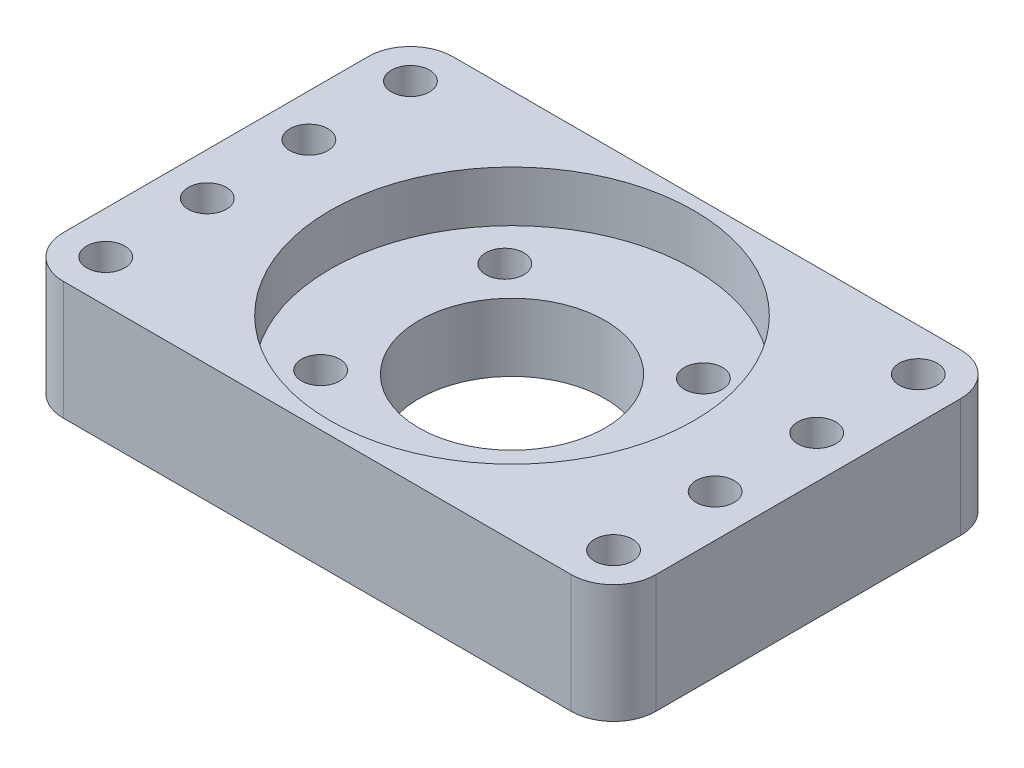
SolidWorks part; units mm, degrees
ref_plane "Front Plane" through (0, 0, 0) normal (0, 0, 1) x (1, 0, 0)
ref_plane "Top Plane" through (0, 0, 0) normal (0, 1, 0) x (1, 0, 0)
ref_plane "Right Plane" through (0, 0, 0) normal (1, 0, 0) x (0, 0, -1)
sketch "Sketch1" plane through (0, 0, 0) normal (0, 1, 0) x (1, 0, 0)
  line L1 (-35, -23) -> (35, -23)
  line L2 (-35, -23) -> (-35, 23)
  line L3 (-35, 23) -> (35, 23)
  line L4 (35, -23) -> (35, 23)
  line L5 (-35, -23) -> (35, 23) construction
  line L6 (-35, 23) -> (35, -23) construction
  circle A0 centre (0, 0) radius 11
  dimension "D1" = 22
  dimension "D2" = 70
  dimension "D3" = 46
extrude "Boss-Extrude1" add sketch "Sketch1" along normal blind 8
sketch "Sketch2" plane through (0, 8, 0) normal (0, 1, 0) x (1, 0, 0)
  line L4 (35, -23) -> (35, 23)
  line L5 (35, 23) -> (-35, 23)
  line L6 (-35, 23) -> (-35, -23)
  line L7 (-35, -23) -> (35, -23)
  line L8 (35, -23) -> (35, 23)
  line L9 (35, 23) -> (-35, 23)
  line L10 (-35, 23) -> (-35, -23)
  line L11 (-35, -23) -> (35, -23)
  circle A0 centre (0, 0) radius 21.5
  dimension "D2" = 43
  dimension "D1" = 0
extrude "Boss-Extrude2" add sketch "Sketch2" along normal blind 6
sketch "Sketch3" plane through (0, 8, 0) normal (0, 1, 0) x (1, 0, 0)
  line L0 (-11.7307, 10.8807) -> (11.7307, 10.8807) construction
  line L1 (35, 23) -> (-35, 23) construction
  line L2 (-11.7307, -10.8807) -> (11.7307, -10.8807) construction
  line L3 (-35, -23) -> (35, -23) construction
  circle A0 centre (0, 0) radius 16
  circle A1 centre (-11.7307, 10.8807) radius 2.25
  circle A2 centre (11.7307, 10.8807) radius 2.25
  circle A3 centre (11.7307, -10.8807) radius 2.25
  circle A4 centre (-11.7307, -10.8807) radius 2.25
  dimension "D1" = 32
  dimension "D2" = 4.5
extrude "Cut-Extrude1" cut sketch "Sketch3" against normal through all contours A0 A3 | A0 A3 | A0 A2 | A0 A2 | A0 A1 | A0 A1 | A0 A4 | A0 A4
sketch "Sketch5" plane through (0, 0, 0) normal (0, -1, 0) x (1, 0, 0)
  line L0 (-11.7307, -10.8807) -> (11.7307, 10.8807) construction
  line L1 (-12.6294, 14.821) -> (-15.5924, 12.0726)
  line L2 (-15.5924, 12.0726) -> (-14.6938, 8.1323)
  line L3 (-14.6938, 8.1323) -> (-10.8321, 6.9404)
  line L4 (-10.8321, 6.9404) -> (-7.8691, 9.6888)
  line L5 (-7.8691, 9.6888) -> (-8.7677, 13.6291)
  line L6 (-8.7677, 13.6291) -> (-12.6294, 14.821)
  line L7 (-10.8321, -6.9404) -> (-14.6938, -8.1323)
  line L8 (-14.6938, -8.1323) -> (-15.5924, -12.0726)
  line L9 (-15.5924, -12.0726) -> (-12.6294, -14.821)
  line L10 (-12.6294, -14.821) -> (-8.7677, -13.6291)
  line L11 (-8.7677, -13.6291) -> (-7.8691, -9.6888)
  line L12 (-7.8691, -9.6888) -> (-10.8321, -6.9404)
  line L13 (10.8321, -6.9404) -> (7.8691, -9.6888)
  line L14 (7.8691, -9.6888) -> (8.7677, -13.6291)
  line L15 (8.7677, -13.6291) -> (12.6294, -14.821)
  line L16 (12.6294, -14.821) -> (15.5924, -12.0726)
  line L17 (15.5924, -12.0726) -> (14.6938, -8.1323)
  line L18 (14.6938, -8.1323) -> (10.8321, -6.9404)
  line L19 (7.8691, 9.6888) -> (10.8321, 6.9404)
  line L20 (10.8321, 6.9404) -> (14.6938, 8.1323)
  line L21 (14.6938, 8.1323) -> (15.5924, 12.0726)
  line L22 (15.5924, 12.0726) -> (12.6294, 14.821)
  line L23 (12.6294, 14.821) -> (8.7677, 13.6291)
  line L24 (8.7677, 13.6291) -> (7.8691, 9.6888)
  line L26 (11.7307, 10.8807) -> (11.7307, -10.8807) construction
  line L27 (11.7307, -10.8807) -> (-11.7307, 10.8807) construction
  circle A0 centre (-11.7307, 10.8807) radius 3.5 construction
  circle A1 centre (-11.7307, -10.8807) radius 3.5 construction
  circle A2 centre (11.7307, -10.8807) radius 3.5 construction
  circle A3 centre (11.7307, 10.8807) radius 3.5 construction
  dimension "D1" = 7
extrude "Cut-Extrude2" cut sketch "Sketch5" against normal blind 3.2
fillet "Fillet1" radius 5 4 edges at (35, 7, -23) (35, 7, 23) (-35, 7, 23) (-35, 7, -23)
sketch "Sketch6" plane through (0, 14, 0) normal (0, 1, 0) x (1, 0, 0)
  line L0 (0, -21.5) -> (0, 21.5) construction
  circle A0 centre (-30, 18) radius 2.25
  circle A1 centre (-30, -18) radius 2.25
  circle A2 centre (30, -18) radius 2.25
  circle A3 centre (30, 18) radius 2.25
  circle A4 centre (-30, 6) radius 2.25
  circle A5 centre (-30, -6) radius 2.25
  circle A6 centre (0, 0) radius 21.5 construction
  circle A7 centre (0, 0) radius 21.5 construction
  circle A8 centre (30, -6) radius 2.25
  circle A9 centre (30, 6) radius 2.25
  dimension "D1" = 4.5
  dimension "D4" = 12
  dimension "D2" = 12
  dimension "D3" = 12
extrude "Cut-Extrude3" cut sketch "Sketch6" against normal through all
